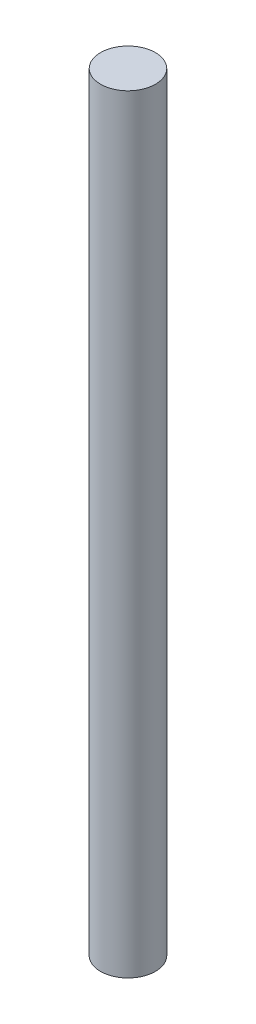
SolidWorks part; units mm, degrees
ref_plane "Front Plane" through (0, 0, 0) normal (0, 0, 1) x (1, 0, 0)
ref_plane "Top Plane" through (0, 0, 0) normal (0, 1, 0) x (1, 0, 0)
ref_plane "Right Plane" through (0, 0, 0) normal (1, 0, 0) x (0, 0, -1)
sketch "Sketch1" plane through (0, 0, 0) normal (0, 1, 0) x (1, 0, 0)
  circle A0 centre (0, 0) radius 6.35
  dimension "D1" = 12.7
extrude "Boss-Extrude1" add sketch "Sketch1" along normal blind 177.8
